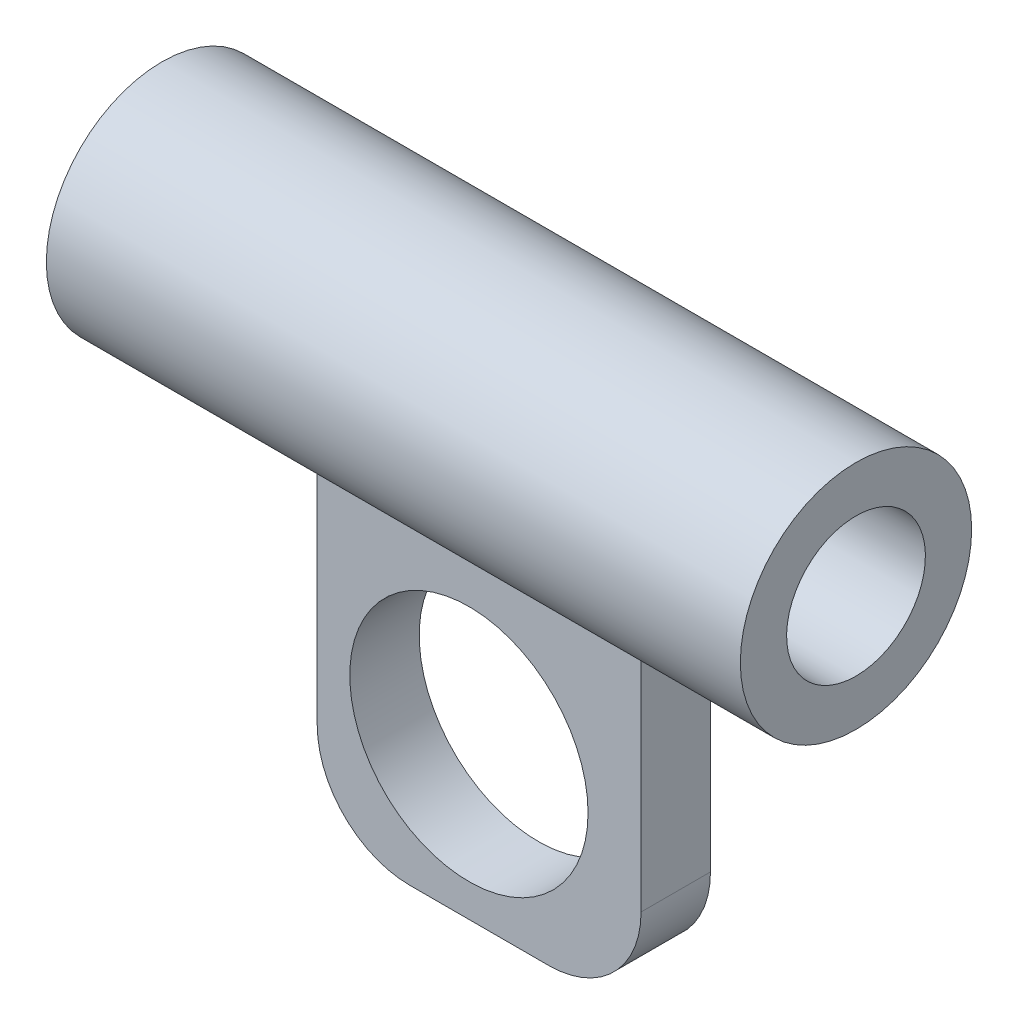
SolidWorks part; units mm, degrees
material "ABS"
ref_plane "Front Plane" through (0, 0, 0) normal (0, 0, 1) x (1, 0, 0)
ref_plane "Top Plane" through (0, 0, 0) normal (0, 1, 0) x (1, 0, 0)
ref_plane "Right Plane" through (0, 0, 0) normal (1, 0, 0) x (0, 0, -1)
sketch "Sketch2" plane through (0, 0, 0) normal (0, 0, 1) x (1, 0, 0)
  line L1 (4, 0) -> (10, 0)
  line L2 (0, 4) -> (0, 16)
  line L3 (4, 20) -> (10, 20)
  line L4 (14, 4) -> (14, 16)
  circle A0 centre (6.558, 6.566) radius 5.15
  arc A1 (4, 0) -> (0, 4) centre (4, 4) cw
  arc A2 (10, 0) -> (14, 4) centre (10, 4) ccw
  arc A3 (10, 20) -> (14, 16) centre (10, 16) cw
  arc A4 (0, 16) -> (4, 20) centre (4, 16) cw
  point P9 (0, 0)
  point P12 (14, 0)
  point P15 (14, 20)
  point P18 (0, 20)
  dimension "D1" = 10.3
  dimension "D4" = 4
  dimension "D2" = 14
  dimension "D3" = 20
extrude "Boss-Extrude1" add sketch "Sketch2" along normal blind 3
ref_plane "Plane1" through (7, 0, 0) normal (-1, 0, 0) x (0, 0, 1)
sketch "Sketch3" plane through (7, 0, 0) normal (-1, 0, 0) x (0, 0, 1)
  circle A0 centre (1.7096, 19.1847) radius 3
  circle A1 centre (1.7096, 19.1847) radius 5
  dimension "D1" = 10
  dimension "D2" = 6
extrude "Boss-Extrude2" add sketch "Sketch3" along normal blind 15 and the other way blind 15
sketch "Sketch5" plane through (22, 0, 0) normal (1, 0, 0) x (0, 0, -1)
  circle A0 centre (-1.7096, 19.1847) radius 3
extrude "Cut-Extrude1" cut sketch "Sketch5" against normal through all
